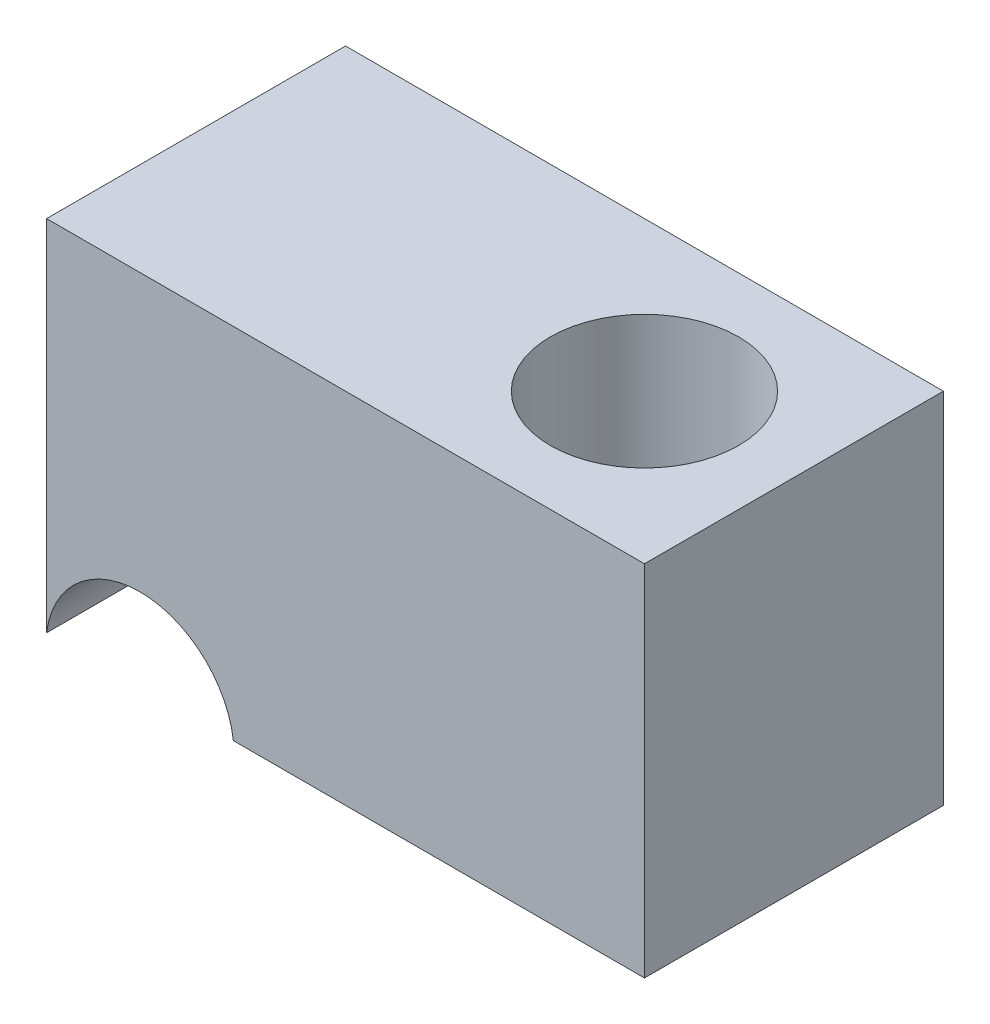
SolidWorks part; units mm, degrees
ref_plane "Front Plane" through (0, 0, 0) normal (0, 0, 1) x (1, 0, 0)
ref_plane "Top Plane" through (0, 0, 0) normal (0, 1, 0) x (1, 0, 0)
ref_plane "Right Plane" through (0, 0, 0) normal (1, 0, 0) x (0, 0, -1)
sketch "Sketch1" plane through (0, 0, 0) normal (0, 0, 1) x (1, 0, 0)
  line L0 (0, 0) -> (-8.7324, 0)
  line L1 (0, 0) -> (0, 7.62)
  line L2 (0, 7.62) -> (-12.7, 7.62)
  line L3 (-12.7, 7.62) -> (-12.7, 0)
  arc A1 (-12.7, 0) -> (-8.7324, 0) centre (-10.7162, -0.254) cw
  dimension "D3" = 0.254
  dimension "D4" = 2
  dimension "D1" = 7.62
  dimension "D2" = 12.7
extrude "Boss-Extrude1" add sketch "Sketch1" along normal blind 6.35
sketch "Sketch2" plane through (0, 0, 0) normal (0, -1, 0) x (1, 0, 0)
  line L0 (-3.175, 0) -> (-3.175, 6.35) construction
  line L1 (-8.7324, 0) -> (0, 0) construction
  line L2 (-8.7324, 6.35) -> (0, 6.35) construction
  line L3 (0, 6.35) -> (0, 0) construction
  circle A0 centre (-3.175, 3.175) radius 1.5991
  dimension "D2" = 3.1982
  dimension "D1" = 3.175
hole_wizard "Ø4.0mm Dowel Hole1" positions "Sketch3" profile "Sketch4" hole size "Ø4.0" standard "ANSI Metric" end condition through all
sketch "Sketch3" plane through (0, 0, 0) normal (0, -1, 0) x (-1, 0, 0)
  point P0 (3.175, -3.175)
sketch "Sketch4" plane through (-3.175, 0, 3.175) normal (1, 0, 0) x (0, 0, -1)
  line L0 (0, 0) -> (0, 7.62)
  line L1 (0, 7.62) -> (2, 7.62)
  line L2 (2, 7.62) -> (2, 0.025)
  line L3 (2, 0.025) -> (2.025, 0)
  line L5 (2.025, 0) -> (0, 0)
  line L6 (-2, 0.025) -> (-2.025, 0) construction
  line L11 (0, -6.35) -> (0, 107.95) construction
  dimension "Thru Hole Dia." = 4
  dimension "Thru Hole Depth" = 7.62
  dimension "Near C'Sink Dia." = 4.05
  dimension "Near C'Sink Angle" = 90
